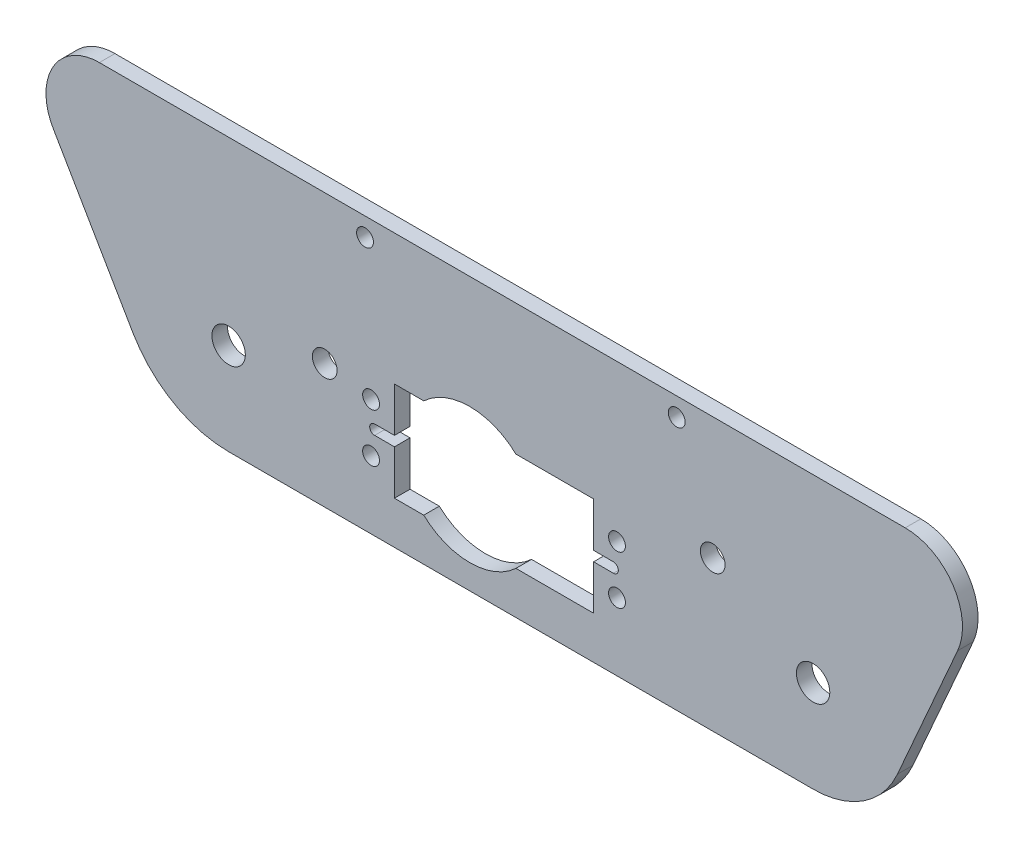
SolidWorks part; units mm, degrees
ref_plane "Front Plane" through (0, 0, 0) normal (0, 0, 1) x (1, 0, 0)
ref_plane "Top Plane" through (0, 0, 0) normal (0, 1, 0) x (1, 0, 0)
ref_plane "Right Plane" through (0, 0, 0) normal (1, 0, 0) x (0, 0, -1)
sketch "Sketch1" plane through (0, 0, 0) normal (0, 0, 1) x (1, 0, 0)
  line L8 (0, 18.9078) -> (120.015, 18.9078) construction
  line L18 (155.2575, 52.1157) -> (-50.9787, 52.1157) construction
  line L37 (0, 0) -> (120.015, 0)
  line L42 (19.7347, 25.5664) -> (0, 18.9078) construction
  line L55 (60.0075, 18.9078) -> (60.0075, 0) construction
  line L58 (138.9371, 55.9257) -> (-26.5433, 55.9257)
  line L60 (137.3256, 11.3022) -> (120.015, 0) construction
  line L61 (-19.6481, 11.3022) -> (0, 0) construction
  line L62 (149.6933, 39.4513) -> (137.3256, 11.3022)
  line L63 (-36.0198, 39.4513) -> (-19.6481, 11.3022)
  line L64 (149.6933, 39.4513) -> (-36.0198, 39.4513) construction
  line L65 (137.3256, 11.3022) -> (-19.6481, 11.3022) construction
  line L66 (120.015, 18.9078) -> (99.4008, 30.8094) construction
  circle A21 centre (120.015, 18.9078) radius 3.429
  circle A22 centre (0, 18.9078) radius 3.429
  arc A25 (137.3256, 11.3022) -> (120.015, 0) centre (120.015, 18.9078) cw
  circle A27 centre (19.7347, 25.5664) radius 2.54
  arc A34 (-19.6481, 11.3022) -> (0, 0) centre (0, 22.7296) ccw
  arc A36 (138.9371, 55.9257) -> (149.6933, 39.4513) centre (138.9371, 44.1772) cw
  arc A37 (-26.5433, 55.9257) -> (-36.0198, 39.4513) centre (-26.5433, 44.9629) ccw
  circle A38 centre (99.4008, 30.8094) radius 2.54
  dimension "D5" = 18.9078
  dimension "D8" = 59.818
  dimension "D3" = 20.6736
  dimension "D11" = 52.1157
  dimension "D13" = 30
  dimension "D2" = 6.858
  dimension "D10" = 5.08
  dimension "D4" = 18.645
  dimension "D6" = 20.8278
  dimension "D7" = 120.015
  dimension "D9" = 3.81
  dimension "D12" = 39.4513
  dimension "D14" = 23.8032
extrude "Boss-Extrude1" add sketch "Sketch1" along normal blind 3.2004
sketch "Sketch2" plane through (0, 0, 0) normal (0, 0, -1) x (-1, 0, 0)
  line L0 (-60.0075, 52.1157) -> (-60.0075, 18.9078) construction
  line L1 (-155.2575, 52.1157) -> (50.9787, 52.1157) construction
  line L14 (0, 18.9078) -> (-120.015, 18.9078) construction
  line L28 (-92.0115, 52.1157) -> (-76.0095, 52.1157) construction
  line L29 (-76.0095, 52.1157) -> (-44.0055, 52.1157) construction
  line L30 (-44.0055, 52.1157) -> (-28.0035, 52.1157) construction
  circle A0 centre (-92.0115, 52.1157) radius 1.7272
  circle A3 centre (-28.0035, 52.1157) radius 1.7272
  point P11 (-36.0045, 52.1157)
  point P16 (-84.0105, 52.1157)
  dimension "D3" = 3.4544
  dimension "D2" = 16.002
  dimension "D4" = 48.006
extrude "Cut-Extrude1" cut sketch "Sketch2" against normal blind 3.2004
sketch "Sketch5" plane through (0, 0, 0) normal (0, 0, -1) x (-1, 0, 0)
  line L0 (0, 18.9078) -> (-120.015, 18.9078) construction
  line L6 (-74.944, 29.0678) -> (-74.944, 8.7478)
  line L7 (-34.05, 29.0678) -> (-34.05, 8.7478)
  line L12 (-54.497, 29.0678) -> (-54.497, 8.7478) construction
  line L13 (-79.747, 13.9078) -> (-79.747, 23.9078) construction
  line L14 (-29.247, 13.9078) -> (-29.247, 23.9078) construction
  line L15 (-79.747, 18.9078) -> (-29.247, 18.9078) construction
  line L21 (-74.944, 8.7478) -> (-34.05, 8.7478)
  line L25 (-74.944, 29.0678) -> (-34.05, 29.0678)
  circle A0 centre (-79.747, 23.9078) radius 1.7272
  circle A1 centre (-29.247, 13.9078) radius 1.7272
  circle A2 centre (-29.247, 23.9078) radius 1.7272
  circle A3 centre (-79.747, 13.9078) radius 1.7272
  circle A6 centre (0, 18.9078) radius 3.429 construction
  point P8 (-44.45, 18.9078)
  point P9 (-54.497, 18.9078)
  dimension "D2" = 3.4544
  dimension "D3" = 40.894
  dimension "D5" = 10.4
  dimension "D1" = 50.5
  dimension "D4" = 20.32
  dimension "D6" = 44.45
extrude "Cut-Extrude3" cut sketch "Sketch5" against normal through all
sketch "Sketch6" plane through (0, 0, 3.2004) normal (0, 0, 1) x (1, 0, 0)
  line L3 (79.747, 18.9078) -> (29.247, 18.9078) construction
  line L4 (29.986, 19.9238) -> (34.05, 19.9238)
  line L5 (29.986, 19.9238) -> (29.986, 17.8918) construction
  line L7 (29.986, 17.8918) -> (34.05, 17.8918)
  line L8 (34.05, 19.9238) -> (34.05, 17.8918)
  line L9 (74.944, 19.9238) -> (79.008, 19.9238)
  line L10 (74.944, 19.9238) -> (74.944, 17.8918)
  line L11 (74.944, 17.8918) -> (79.008, 17.8918)
  line L12 (79.008, 19.9238) -> (79.008, 17.8918) construction
  line L13 (34.05, 8.7478) -> (34.05, 29.0678) construction
  line L14 (74.944, 29.0678) -> (74.944, 8.7478) construction
  arc A6 (79.008, 19.9238) -> (79.008, 17.8918) centre (79.008, 18.9078) cw
  arc A7 (29.986, 19.9238) -> (29.986, 17.8918) centre (29.986, 18.9078) ccw
  point P22 (34.05, 18.9078)
  point P23 (74.944, 18.9078)
  dimension "D4" = 4.064
  dimension "D5" = 2.032
extrude "Cut-Extrude4" cut sketch "Sketch6" against normal up to surface (3.2004 mm away) up to face at (78.0198, 23.9078, 0)
sketch "Sketch9" plane through (0, 0, 0) normal (0, 0, -1) x (-1, 0, 0)
  line L1 (-79.747, 18.9078) -> (-29.247, 18.9078) construction
  circle A0 centre (-49.53, 18.9078) radius 13.8852
  dimension "D1" = 27.7704
  dimension "D2" = 5.08
extrude "Cut-Extrude7" cut sketch "Sketch9" against normal up to surface (3.2004 mm away) up to face at (54.497, 18.9078, 3.2004)
